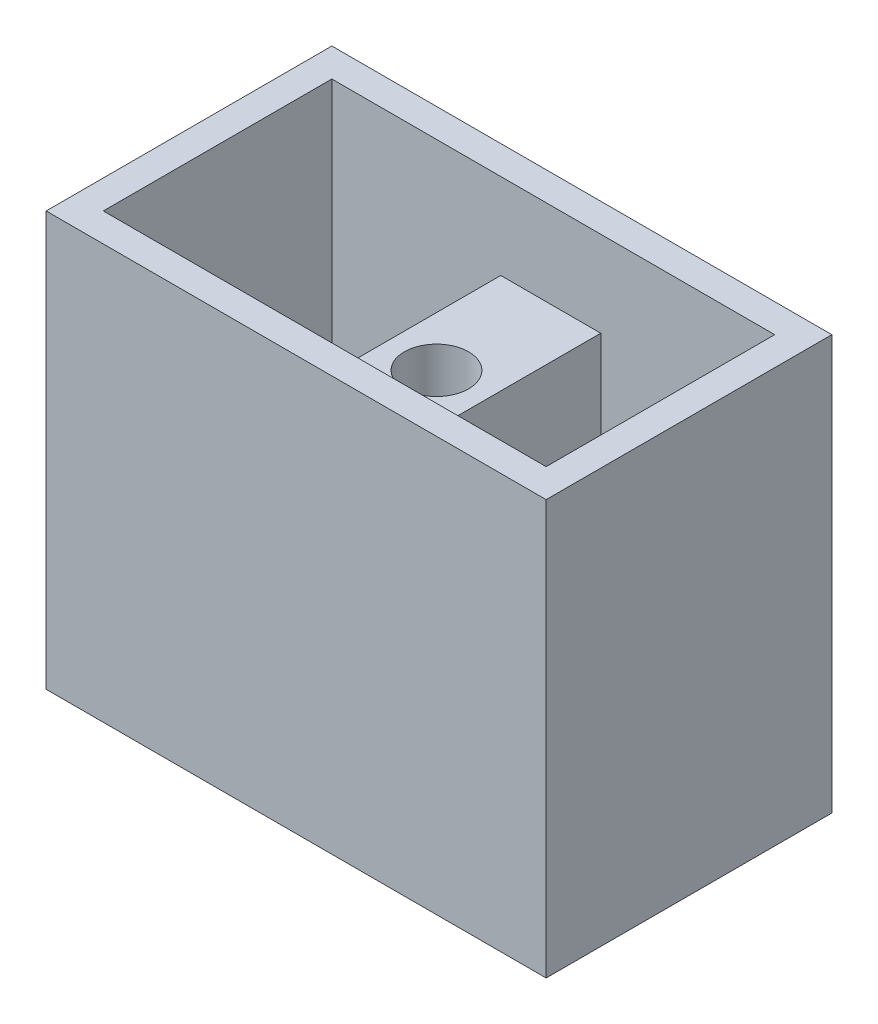
SolidWorks part; units mm, degrees
ref_plane "Front Plane" through (0, 0, 0) normal (0, 0, 1) x (1, 0, 0)
ref_plane "Top Plane" through (0, 0, 0) normal (0, 1, 0) x (1, 0, 0)
ref_plane "Right Plane" through (0, 0, 0) normal (1, 0, 0) x (0, 0, -1)
sketch "Sketch1" plane through (0, 0, 0) normal (0, 1, 0) x (1, 0, 0)
  line L1 (0, 0) -> (175, 0)
  line L2 (0, 0) -> (0, 100)
  line L3 (0, 100) -> (175, 100)
  line L4 (175, 0) -> (175, 100)
  dimension "D1" = 175
  dimension "D2" = 100
extrude "Boss-Extrude1" add sketch "Sketch1" along normal blind 145
sketch "Sketch2" plane through (0, 145, 0) normal (0, 1, 0) x (1, 0, 0)
  line L10 (69.1133, 90) -> (69.1133, 10)
  line L11 (104.1133, 90) -> (104.1133, 10)
  line L12 (86.6133, 86.4407) -> (86.6133, -12.5064) construction
  line L13 (69.1133, 90) -> (10, 90)
  line L14 (10, 10) -> (165, 10)
  line L15 (165, 10) -> (165, 90)
  line L16 (165, 90) -> (10, 90)
  line L17 (10, 90) -> (10, 10)
  line L18 (10, 10) -> (69.1133, 10)
  line L19 (165, 10) -> (165, 90)
  line L20 (165, 90) -> (104.1133, 90)
  line L21 (10, 90) -> (10, 10)
  line L22 (104.1133, 10) -> (165, 10)
  circle A0 centre (86.6133, 50) radius 11.25
  point P13 (104.1133, 50)
  dimension "D3" = 22.5
  dimension "D2" = 35
  dimension "D1" = 10
extrude "Cut-Extrude1" cut sketch "Sketch2" against normal blind 145
sketch "Sketch4" plane through (0, 145, 0) normal (0, 1, 0) x (1, 0, 0)
  line L3 (69.1133, 90) -> (104.1133, 90)
  line L4 (69.1133, 90) -> (69.1133, 10)
  line L5 (69.1133, 10) -> (104.1133, 10)
  line L6 (104.1133, 90) -> (104.1133, 10)
extrude "Cut-Extrude2" cut sketch "Sketch4" against normal blind 30
sketch "Sketch5" plane through (0, 0, 0) normal (0, -1, 0) x (1, 0, 0)
  line L1 (69.1133, -10) -> (104.1133, -10)
  line L2 (69.1133, -10) -> (69.1133, -90)
  line L3 (69.1133, -90) -> (104.1133, -90)
  line L4 (104.1133, -10) -> (104.1133, -90)
extrude "Cut-Extrude3" cut sketch "Sketch5" against normal blind 30
